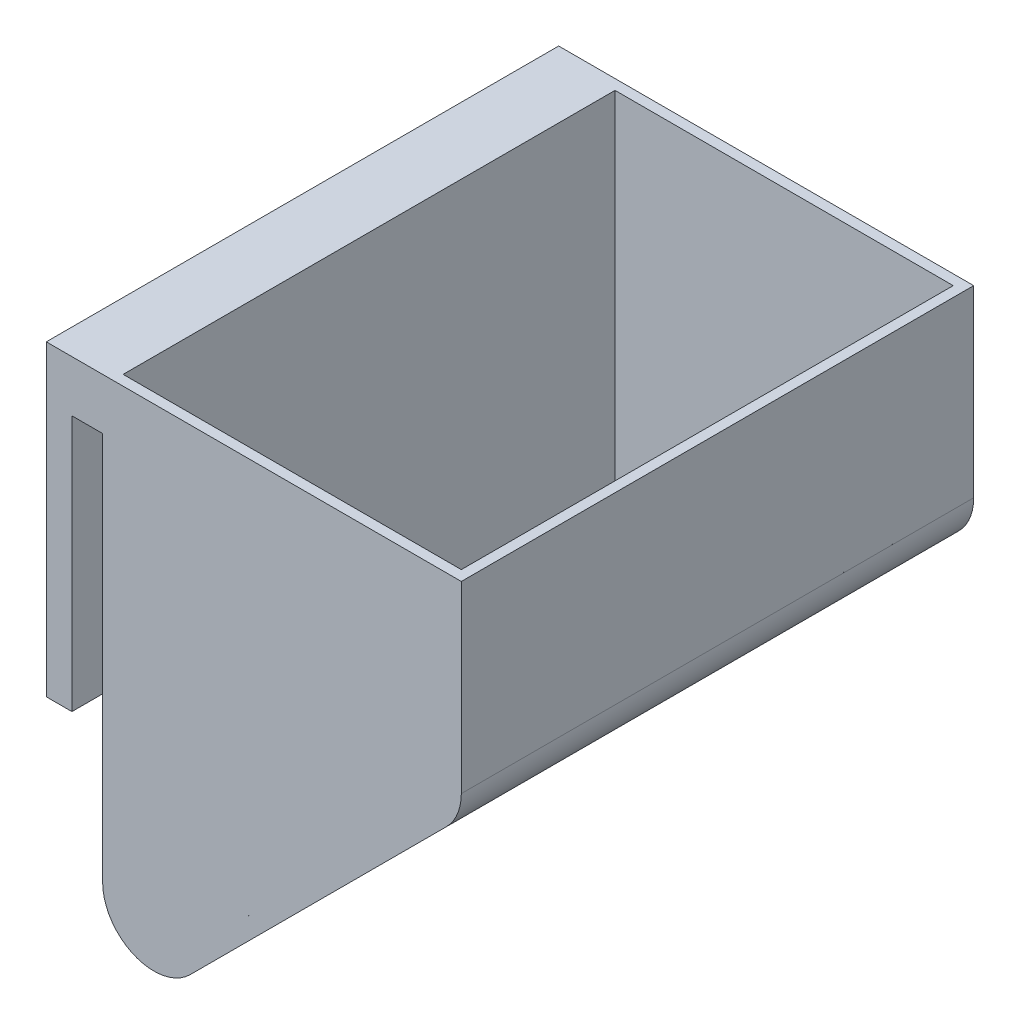
SolidWorks part; units mm, degrees
ref_plane "Front Plane" through (0, 0, 0) normal (0, 0, 1) x (1, 0, 0)
ref_plane "Top Plane" through (0, 0, 0) normal (0, 1, 0) x (1, 0, 0)
ref_plane "Right Plane" through (0, 0, 0) normal (1, 0, 0) x (0, 0, -1)
sketch "Sketch1" plane through (0, 0, 0) normal (0, 0, 1) x (1, 0, 0)
  line L2 (-11, 0) -> (-11, -60)
  line L3 (-11, -60) -> (-6, -60)
  line L4 (-6, -60) -> (-6, -10)
  line L5 (-6, -10) -> (0, -10)
  line L6 (0, -10) -> (0, -110)
  line L7 (70, 0) -> (70, -40)
  line L8 (0, -110) -> (70, -40)
  line L9 (-11, 0) -> (70, 0)
  dimension "D2" = 60
  dimension "100" = 100
  dimension "D4" = 5
  dimension "D5" = 135
  dimension "D6" = 6
extrude "Boss-Extrude2" add sketch "Sketch1" along normal blind 100
sketch "Sketch2" plane through (0, 0, 0) normal (0, 1, 0) x (1, 0, 0)
  line L1 (2, -2) -> (68, -2)
  line L2 (2, -2) -> (2, -98)
  line L3 (2, -98) -> (68, -98)
  line L4 (68, -2) -> (68, -98)
  line L5 (35, -98) -> (35, -2) construction
  line L6 (2, -50) -> (68, -50) construction
  point P424 (35, -50)
  dimension "D1" = 2
  dimension "D2" = 2
  dimension "D3" = 2
  dimension "D4" = 2
extrude "Cut-Extrude5" cut sketch "Sketch2" against normal blind 10
ref_plane "Plane11" through (2, -10, 98) normal (1, 0, 0) x (0, 0, -1)
ref_plane "Plane12" through (2, -10, 98) normal (0, 1, 0) x (1, 0, 0)
ref_plane "Plane13" through (2, 0, 98) normal (0, 0, 1) x (1, 0, 0)
sketch "Sketch5" plane through (2, 0, 98) normal (0, 0, 1) x (1, 0, 0)
  line L0 (0, 0) -> (0, -103.7574)
  line L1 (0, -28.15) -> (0, 8.15) construction
  line L2 (0, -103.7574) -> (66, -37.7639)
  line L3 (66, -37.7639) -> (66, 0)
  line L4 (0, 0) -> (66, 0)
  line L5 (-2, -110) -> (68, -40) construction
  dimension "D1" = 2
  dimension "D2" = 3
  dimension "D3" = 3
extrude "Cut-Extrude6" cut sketch "Sketch5" against normal blind 96
fillet "Fillet6" radius 10 4 edges at (68, -37.7639, 50) (70, -40, 50) (2, -103.7574, 50) (0, -110, 50)
